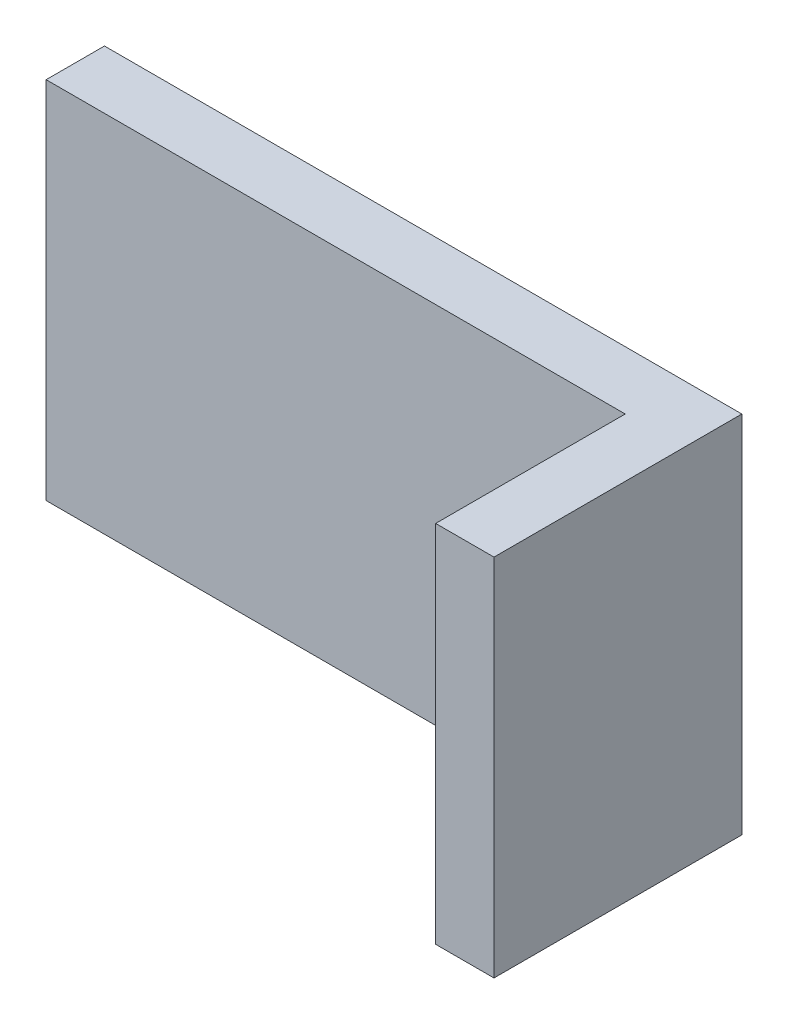
SolidWorks part; units mm, degrees
ref_plane "Front Plane" through (0, 0, 0) normal (0, 0, 1) x (1, 0, 0)
ref_plane "Top Plane" through (0, 0, 0) normal (0, 1, 0) x (1, 0, 0)
ref_plane "Right Plane" through (0, 0, 0) normal (1, 0, 0) x (0, 0, -1)
sketch "Sketch1" plane through (0, 0, 0) normal (0, 1, 0) x (1, 0, 0)
  line L0 (0, 0) -> (-79.4286, 0)
  line L1 (-79.4286, 0) -> (-79.4286, 8)
  line L2 (-79.4286, 8) -> (8, 8)
  line L3 (8, 8) -> (8, -26)
  line L4 (8, -26) -> (0, -26)
  line L5 (0, -26) -> (0, 0)
  dimension "D1" = 8
  dimension "D2" = 8
extrude "Boss-Extrude1" add sketch "Sketch1" along normal mid plane 50
